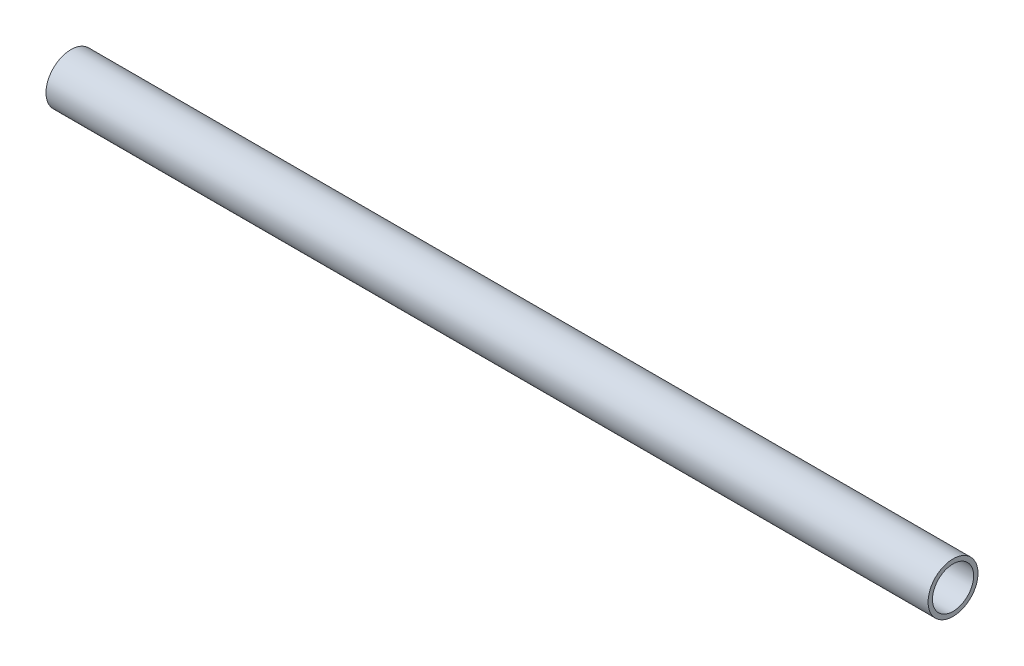
SolidWorks part; units mm, degrees
ref_plane "Front Plane" through (0, 0, 0) normal (0, 0, 1) x (1, 0, 0)
ref_plane "Top Plane" through (0, 0, 0) normal (0, 1, 0) x (1, 0, 0)
ref_plane "Right Plane" through (0, 0, 0) normal (1, 0, 0) x (0, 0, -1)
sketch "Sketch2" plane through (0, 0, 0) normal (0, 0, 1) x (1, 0, 0)
  line L1 (-82.7561, 647.7024) -> (-194.9577, 647.7024)
other "Pipe 0.5 SCH 40(1)"
ref_plane "Plane1" through (-82.7561, 647.7024, 0) normal (-1, 0, 0) x (0, -1, 0)
sketch "Sketch1" plane through (-82.7561, 647.7024, 0) normal (-1, 0, 0) x (0, -1, 0)
  circle A0 centre (0, 0) radius 2.6162
  circle A1 centre (0, 0) radius 3.175
  point P5 (0, 0)
  dimension "In_dia" = 5.2324
  dimension "Out_dia" = 6.35
